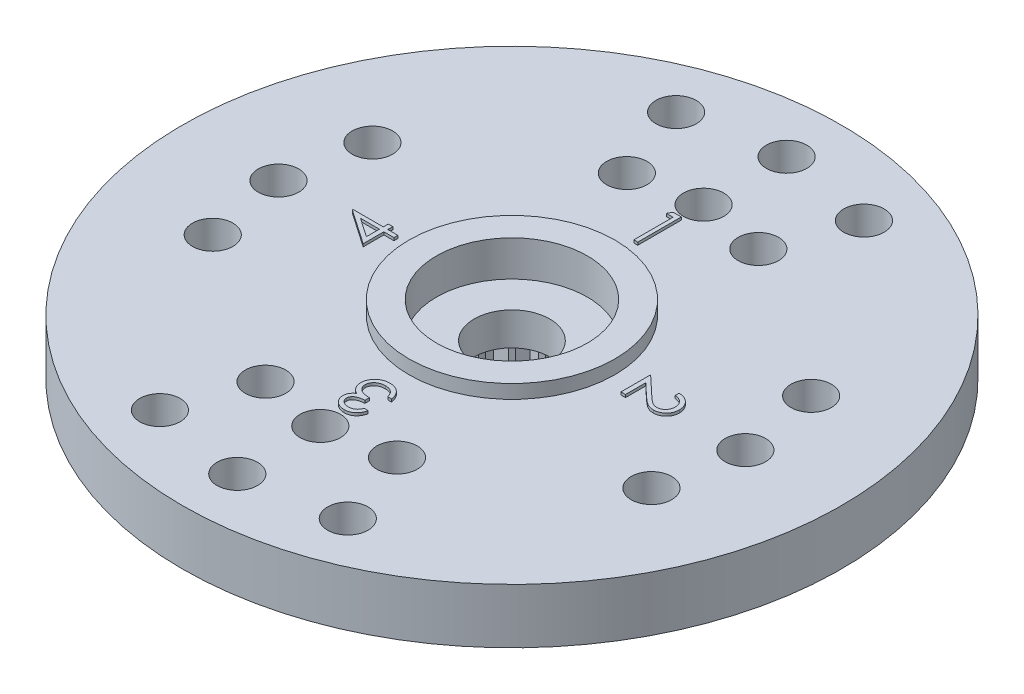
SolidWorks part; units mm, degrees
ref_plane "Front Plane" through (0, 0, 0) normal (0, 0, 1) x (1, 0, 0)
ref_plane "Top Plane" through (0, 0, 0) normal (0, 1, 0) x (1, 0, 0)
ref_plane "Right Plane" through (0, 0, 0) normal (1, 0, 0) x (0, 0, -1)
sketch "Sketch1" plane through (0, 0, 0) normal (0, 1, 0) x (1, 0, 0)
  line L0 (0, 12) -> (0, -12) construction
  line L1 (-12, 0) -> (12, 0) construction
  line L2 (0, 0) -> (3.4202, 9.3969) construction
  line L3 (-3.4202, 9.3969) -> (0, 0) construction
  line L4 (0, 0) -> (7.9874, 2.9072) construction
  line L5 (0, 0) -> (7.9874, -2.9072) construction
  circle A0 centre (0, 0) radius 12
  circle A1 centre (0, 0) radius 1.375
  circle A2 centre (0, 0) radius 7 construction
  circle A3 centre (0, 0) radius 10 construction
  circle A4 centre (0, 0) radius 8.5 construction
  circle A5 centre (0, 10) radius 0.7366
  circle A6 centre (-3.4202, 9.3969) radius 0.7366
  circle A7 centre (3.4202, 9.3969) radius 0.7366
  circle A8 centre (0, 6.9777) radius 0.7366
  circle A9 centre (-2.3941, 6.5778) radius 0.7366
  circle A10 centre (2.3941, 6.5778) radius 0.7366
  circle A11 centre (8.5, 0) radius 0.7366
  circle A12 centre (7.9874, 2.9072) radius 0.7366
  circle A13 centre (7.9874, -2.9072) radius 0.7366
  circle A14 centre (-2.3941, -6.5778) radius 0.7366
  circle A15 centre (0, -6.9777) radius 0.7366
  circle A16 centre (2.3941, -6.5778) radius 0.7366
  circle A17 centre (3.4202, -9.3969) radius 0.7366
  circle A18 centre (0, -10) radius 0.7366
  circle A19 centre (-3.4202, -9.3969) radius 0.7366
  circle A20 centre (-7.9874, -2.9072) radius 0.7366
  circle A21 centre (-8.5, 0) radius 0.7366
  circle A22 centre (-7.9874, 2.9072) radius 0.7366
  dimension "D1" = 24
  dimension "D2" = 2.75
  dimension "D3" = 14
  dimension "D4" = 20
  dimension "D5" = 17
  dimension "D6" = 1.4732
  dimension "D7" = 1.4732
  dimension "D9" = 1.4732
  dimension "D11" = 1.4732
  dimension "D12" = 1.4732
  dimension "D13" = 1.4732
  dimension "D16" = 1.4732
  dimension "D17" = 1.4732
  dimension "D18" = 1.4732
  dimension "D8" = 20
  dimension "D10" = 20
  dimension "D14" = 20
  dimension "D15" = 20
extrude "Boss-Extrude1" add sketch "Sketch1" along normal blind 2
sketch "Sketch2" plane through (0, 2, 0) normal (0, 1, 0) x (1, 0, 0)
  circle A0 centre (0, 0) radius 3.75
  circle A1 centre (0, 0) radius 2.75
  dimension "D1" = 7.5
  dimension "D2" = 1
extrude "Boss-Extrude2" add sketch "Sketch2" along normal blind 0.5
sketch "Sketch3" plane through (0, 2, 0) normal (0, 1, 0) x (1, 0, 0)
  circle A0 centre (0, 0) radius 1.375 construction
  circle A1 centre (0, 0) radius 2.75 construction
  circle A2 centre (0, 0) radius 1.375
  circle A3 centre (0, 0) radius 2.75
extrude "Cut-Extrude1" cut sketch "Sketch3" against normal blind 0.8
sketch "Sketch4" plane through (0, 0, 0) normal (0, -1, 0) x (1, 0, 0)
  circle A0 centre (0, 0) radius 4.5
  circle A1 centre (0, 0) radius 2.5
  dimension "D1" = 9
  dimension "D2" = 2
extrude "Boss-Extrude3" add sketch "Sketch4" along normal blind 2.5
sketch "Sketch5" plane through (0, -2.5, 0) normal (0, -1, 0) x (1, 0, 0)
  line L0 (0, 0) -> (0, 0.6245) construction
  line L1 (0, 3) -> (-0.299, 2.4821)
  line L2 (0, 3) -> (0.299, 2.4821)
  line L3 (0.9271, 2.8532) -> (0.4826, 2.453)
  line L4 (0.9271, 2.8532) -> (1.0514, 2.2682)
  line L5 (1.7634, 2.4271) -> (1.217, 2.1838)
  line L6 (1.7634, 2.4271) -> (1.7008, 1.8323)
  line L7 (2.4271, 1.7634) -> (1.8323, 1.7008)
  line L8 (2.4271, 1.7634) -> (2.1838, 1.217)
  line L9 (2.8532, 0.9271) -> (2.2682, 1.0514)
  line L10 (2.8532, 0.9271) -> (2.453, 0.4826)
  line L11 (3, 0) -> (2.4821, 0.299)
  line L12 (3, 0) -> (2.4821, -0.299)
  line L13 (2.8532, -0.9271) -> (2.453, -0.4826)
  line L14 (2.8532, -0.9271) -> (2.2682, -1.0514)
  line L15 (2.4271, -1.7634) -> (2.1838, -1.217)
  line L16 (2.4271, -1.7634) -> (1.8323, -1.7008)
  line L17 (1.7634, -2.4271) -> (1.7008, -1.8323)
  line L18 (1.7634, -2.4271) -> (1.217, -2.1838)
  line L19 (0.9271, -2.8532) -> (1.0514, -2.2682)
  line L20 (0.9271, -2.8532) -> (0.4826, -2.453)
  line L21 (0, -3) -> (0.299, -2.4821)
  line L22 (0, -3) -> (-0.299, -2.4821)
  line L23 (-0.9271, -2.8532) -> (-0.4826, -2.453)
  line L24 (-0.9271, -2.8532) -> (-1.0514, -2.2682)
  line L25 (-1.7634, -2.4271) -> (-1.217, -2.1838)
  line L26 (-1.7634, -2.4271) -> (-1.7008, -1.8323)
  line L27 (-2.4271, -1.7634) -> (-1.8323, -1.7008)
  line L28 (-2.4271, -1.7634) -> (-2.1838, -1.217)
  line L29 (-2.8532, -0.9271) -> (-2.2682, -1.0514)
  line L30 (-2.8532, -0.9271) -> (-2.453, -0.4826)
  line L31 (-3, 0) -> (-2.4821, -0.299)
  line L32 (-3, 0) -> (-2.4821, 0.299)
  line L33 (-2.8532, 0.9271) -> (-2.453, 0.4826)
  line L34 (-2.8532, 0.9271) -> (-2.2682, 1.0514)
  line L35 (-2.4271, 1.7634) -> (-2.1838, 1.217)
  line L36 (-2.4271, 1.7634) -> (-1.8323, 1.7008)
  line L37 (-1.7634, 2.4271) -> (-1.7008, 1.8323)
  line L38 (-1.7634, 2.4271) -> (-1.217, 2.1838)
  line L39 (-0.9271, 2.8532) -> (-1.0514, 2.2682)
  line L40 (-0.9271, 2.8532) -> (-0.4826, 2.453)
  circle A0 centre (0, 0) radius 2.5 construction
  arc A1 (-2.1838, 1.217) -> (-2.2682, 1.0514) centre (0, 0) ccw
  arc A2 (-1.7008, 1.8323) -> (-1.8323, 1.7008) centre (0, 0) ccw
  arc A3 (-1.0514, 2.2682) -> (-1.217, 2.1838) centre (0, 0) ccw
  arc A4 (-0.299, 2.4821) -> (-0.4826, 2.453) centre (0, 0) ccw
  arc A5 (0.4826, 2.453) -> (0.299, 2.4821) centre (0, 0) ccw
  arc A6 (1.217, 2.1838) -> (1.0514, 2.2682) centre (0, 0) ccw
  arc A7 (1.8323, 1.7008) -> (1.7008, 1.8323) centre (0, 0) ccw
  arc A8 (2.2682, 1.0514) -> (2.1838, 1.217) centre (0, 0) ccw
  arc A9 (2.4821, 0.299) -> (2.453, 0.4826) centre (0, 0) ccw
  arc A10 (2.453, -0.4826) -> (2.4821, -0.299) centre (0, 0) ccw
  arc A11 (2.1838, -1.217) -> (2.2682, -1.0514) centre (0, 0) ccw
  arc A12 (1.7008, -1.8323) -> (1.8323, -1.7008) centre (0, 0) ccw
  arc A13 (1.0514, -2.2682) -> (1.217, -2.1838) centre (0, 0) ccw
  arc A14 (0.299, -2.4821) -> (0.4826, -2.453) centre (0, 0) ccw
  arc A15 (-0.4826, -2.453) -> (0, -2.5) centre (0, 0) ccw
  arc A16 (-1.217, -2.1838) -> (-1.0514, -2.2682) centre (0, 0) ccw
  arc A17 (-1.8323, -1.7008) -> (-1.7008, -1.8323) centre (0, 0) ccw
  arc A18 (-2.2682, -1.0514) -> (-2.1838, -1.217) centre (0, 0) ccw
  arc A19 (-2.4821, -0.299) -> (-2.453, -0.4826) centre (0, 0) ccw
  arc A20 (-2.453, 0.4826) -> (-2.4821, 0.299) centre (0, 0) ccw
  point P68 (0, 0)
  circle M5 centre (0, 0) radius 2.5
  dimension "D1" = 30
  dimension "D2" = 3
  dimension "D3" = 20
extrude "Cut-Extrude3" cut sketch "Sketch5" against normal up to surface (2.5 mm away) contours L36 L35 M5 | L34 L33 M5 | L32 L31 M5 | L30 L29 M5 | L28 L27 M5 | L26 L25 M5 | L24 L23 M5 | L0 L21 M5 | L22 L0 M5 | L20 L19 M5 | L18 L17 M5 | L16 L15 M5 | L14 L13 M5 | L12 L11 M5 | L10 L9 M5 | L8 L7 M5 | L6 L5 M5 | L4 L3 M5 | L0 L2 M5 | L0 L1 M5 | L40 L39 M5 | L38 L37 M5
sketch "Sketch6" plane through (0, 2, 0) normal (0, 1, 0) x (1, 0, 0)
  line L1 (4.5, -4.5) -> (-4.5, -4.5) construction
  line L2 (4.5, -4.5) -> (4.5, 4.5) construction
  line L3 (4.5, 4.5) -> (-4.5, 4.5) construction
  line L4 (-4.5, -4.5) -> (-4.5, 4.5) construction
  line L5 (4.5, -4.5) -> (-4.5, 4.5) construction
  line L6 (4.5, 4.5) -> (-4.5, -4.5) construction
  circle A0 centre (0, 0) radius 4.5 construction
  text T0 "1" font "Century Gothic" height in points 6
  text T1 "2" font "Century Gothic" height in points 6
  text T2 "3" font "Century Gothic" height in points 6
  text T3 "4" font "Century Gothic" height in points 6
  dimension "D1" = 9
  dimension "D2" = 9
  dimension "D3" = 9
extrude "Boss-Extrude4" add sketch "Sketch6" along normal blind 0.1
